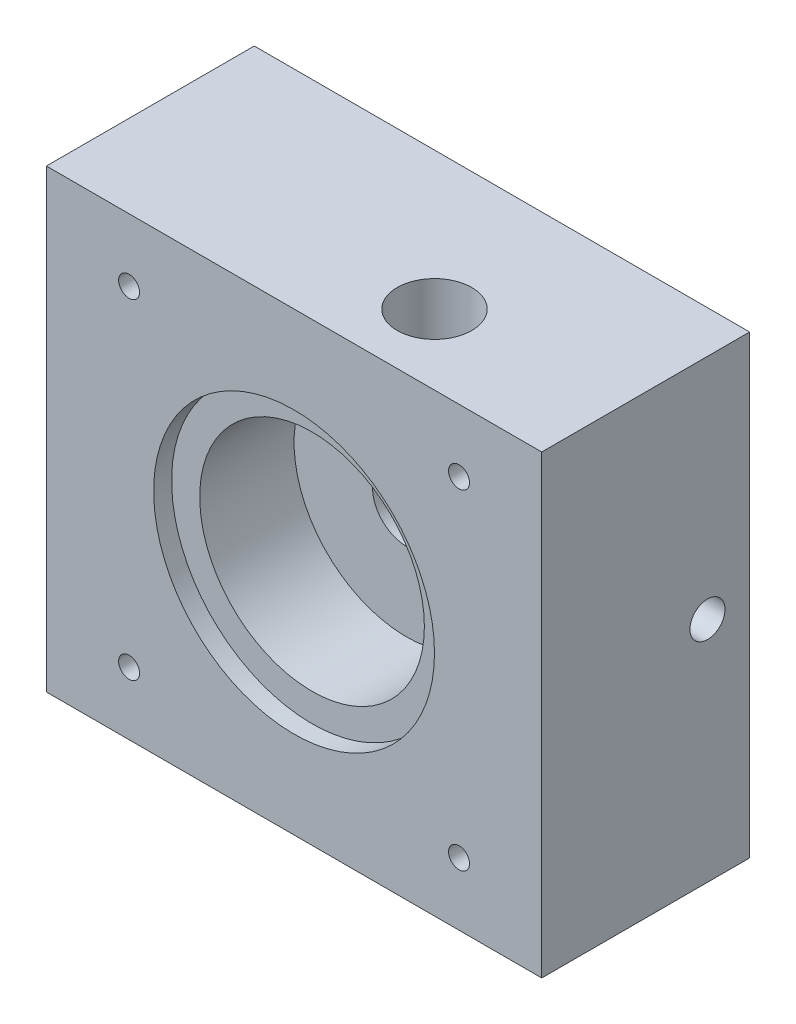
SolidWorks part; units mm, degrees
ref_plane "Front Plane" through (0, 0, 0) normal (0, 0, 1) x (1, 0, 0)
ref_plane "Top Plane" through (0, 0, 0) normal (0, 1, 0) x (1, 0, 0)
ref_plane "Right Plane" through (0, 0, 0) normal (1, 0, 0) x (0, 0, -1)
sketch "Sketch1" plane through (0, 0, 0) normal (0, 0, 1) x (1, 0, 0)
  line L0 (0, 25.75) -> (0, -25.75) construction
  line L1 (-28, 0) -> (28, 0) construction
  line L2 (28, 25.75) -> (-28, 25.75)
  line L3 (-28, 25.75) -> (-28, -25.75)
  line L4 (-28, -25.75) -> (28, -25.75)
  line L5 (28, -25.75) -> (28, 25.75)
  point P4 (0, 0)
  point P8 (0, 0)
  dimension "D1" = 56
  dimension "D2" = 51.5
extrude "Boss-Extrude1" add sketch "Sketch1" along normal blind 23.5
sketch "Sketch2" plane through (0, 0, 23.5) normal (0, 0, 1) x (1, 0, 0)
  circle A0 centre (0, 0) radius 15.875
  dimension "D1" = 31.75
extrude "Cut-Extrude1" cut sketch "Sketch2" against normal blind 2.032
sketch "Sketch3" plane through (0, 0, 21.468) normal (0, 0, 1) x (1, 0, 0)
  circle A0 centre (0, 0) radius 12.7
  dimension "D1" = 25.4
extrude "Cut-Extrude2" cut sketch "Sketch3" against normal blind 10.668
sketch "Sketch4" plane through (0, 0, 10.8) normal (0, 0, 1) x (1, 0, 0)
  circle A0 centre (0, 0) radius 3.8354
  dimension "D1" = 7.6708
extrude "Cut-Extrude3" cut sketch "Sketch4" against normal through all
sketch "Sketch5" plane through (0, 0, 0) normal (0, 0, -1) x (-1, 0, 0)
  circle A0 centre (0, 0) radius 6.35
  dimension "D1" = 12.7
extrude "Cut-Extrude4" cut sketch "Sketch5" against normal blind 2.794
sketch "Sketch6" plane through (0, 25.75, 0) normal (0, 1, 0) x (1, 0, 0)
  line L0 (0, -23.5) -> (0, -15.5625) construction
  line L1 (28, -23.5) -> (-28, -23.5) construction
  line L2 (0, -15.5625) -> (7.9375, -15.5625) construction
  circle A0 centre (7.9375, -15.5625) radius 4.2164
  dimension "D3" = 8.4328
  dimension "D1" = 7.9375
  dimension "D2" = 7.9375
extrude "Cut-Extrude5" cut sketch "Sketch6" against normal blind 25.4
sketch "Sketch7" plane through (0, 0, 0) normal (0, 0, -1) x (-1, 0, 0)
  line L0 (-28, -25.75) -> (-28, 25.75) construction
  circle A0 centre (-18.475, 0) radius 1.9844
  dimension "D2" = 3.9688
  dimension "D1" = 9.525
extrude "Cut-Extrude6" cut sketch "Sketch7" against normal blind 6.35
mirror "Mirror1" about plane through (0, 0, 0) normal (1, 0, 0) of "Cut-Extrude6"
sketch "Sketch8" plane through (28, 0, 0) normal (1, 0, 0) x (0, 0, -1)
  circle A0 centre (-4.7625, 0) radius 1.9844
  dimension "D1" = 3.9688
  dimension "D2" = 4.7625
extrude "Cut-Extrude7" cut sketch "Sketch8" against normal blind 11.1125
mirror "Mirror2" about plane through (0, 0, 0) normal (1, 0, 0) of "Cut-Extrude7"
sketch "Sketch9" plane through (0, 0, 23.5) normal (0, 0, 1) x (1, 0, 0)
  line L0 (-28, -25.75) -> (28, -25.75) construction
  line L1 (-25, -25.75) -> (25, -25.75) construction
  line L2 (-25, -25.75) -> (-25, 25.75) construction
  line L4 (25, -25.75) -> (25, 25) construction
  line L6 (0, 0) -> (0, -25.75) construction
  line L8 (-25, -25) -> (25, -25) construction
  line L9 (-25, -25) -> (-25, 25) construction
  line L10 (-25, 25) -> (25, 25) construction
  line L11 (25, -25) -> (25, 25) construction
  line L12 (-25, -25) -> (25, 25) construction
  line L13 (-25, 25) -> (25, -25) construction
  circle A0 centre (18.65, 18.65) radius 1.1811
  point P11 (0, -25.75)
  dimension "D5" = 2.3622
  dimension "D1" = 25
  dimension "D2" = 50
  dimension "D3" = 6.35
  dimension "D4" = 6.35
extrude "Cut-Extrude8" cut sketch "Sketch9" against normal through all
mirror "Mirror3" about plane through (0, 0, 0) normal (0, 1, 0) of "Cut-Extrude8"
mirror "Mirror4" about plane through (0, 0, 0) normal (1, 0, 0) of "Mirror3", "Cut-Extrude8"
